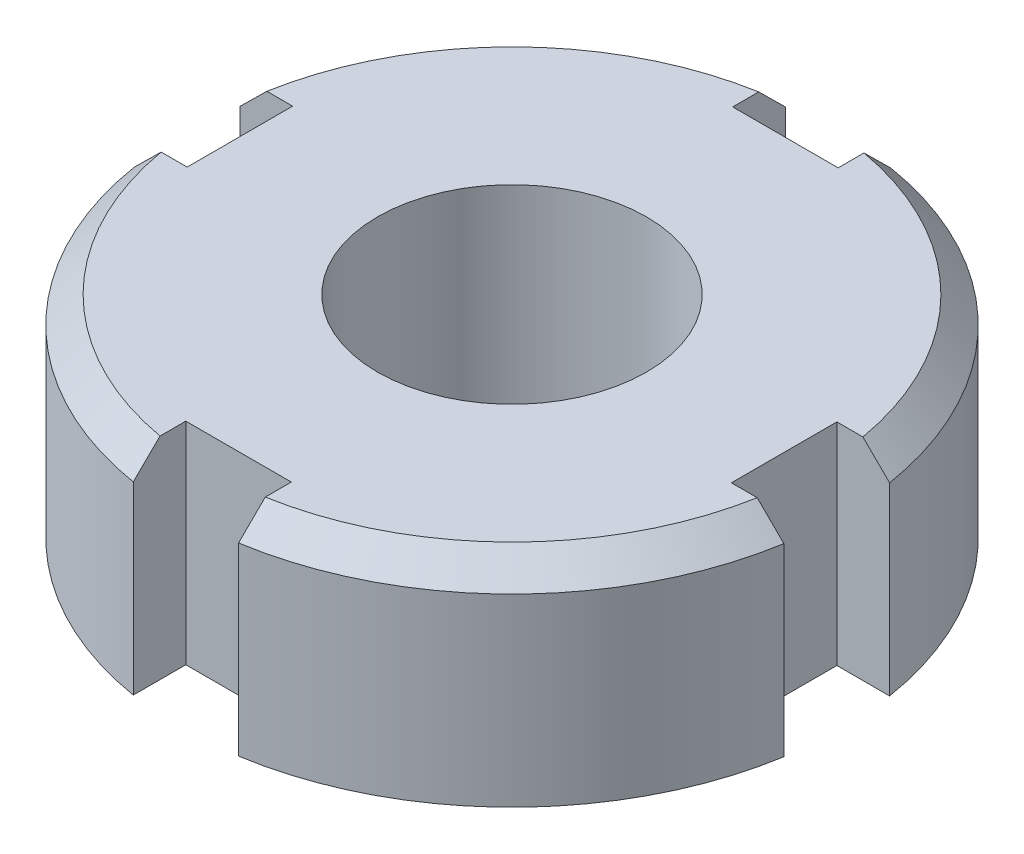
SolidWorks part; units mm, degrees
material "Plain Carbon Steel"
ref_plane "Front Plane" through (0, 0, 0) normal (0, 0, 1) x (1, 0, 0)
ref_plane "Top Plane" through (0, 0, 0) normal (0, 1, 0) x (1, 0, 0)
ref_plane "Right Plane" through (0, 0, 0) normal (1, 0, 0) x (0, 0, -1)
sketch "Sketch1" plane through (0, 0, 0) normal (0, 1, 0) x (1, 0, 0)
  circle A0 centre (0, 0) radius 12.5
  dimension "D1" = 25
extrude "Boss-Extrude1" add sketch "Sketch1" along normal mid plane 8
sketch "Sketch2" plane through (0, 0, 0) normal (0, 1, 0) x (1, 0, 0)
  line L2 (2.0251, 12.343) -> (2.0251, 10.343)
  line L3 (2.0251, 10.343) -> (-1.9749, 10.343)
  line L4 (-1.9749, 12.343) -> (-1.9749, 10.343)
  line L5 (-1.9749, 12.343) -> (-1.9749, 10.343) construction
  line L6 (12.343, 1.9749) -> (10.343, 1.9749)
  line L7 (12.343, -2.0251) -> (10.343, -2.0251)
  line L8 (10.343, -2.0251) -> (10.343, 1.9749)
  line L9 (1.9749, -12.343) -> (1.9749, -10.343)
  line L10 (-2.0251, -12.343) -> (-2.0251, -10.343)
  line L11 (-2.0251, -10.343) -> (1.9749, -10.343)
  line L12 (-12.343, -1.9749) -> (-10.343, -1.9749)
  line L13 (-12.343, 2.0251) -> (-10.343, 2.0251)
  line L14 (-10.343, 2.0251) -> (-10.343, -1.9749)
  circle A0 centre (0, 0) radius 12.5 construction
  arc A1 (2.0251, 12.3349) -> (-1.9749, 12.343) centre (0, 0) ccw
  arc A2 (12.3349, -2.0251) -> (12.343, 1.9749) centre (0, 0) ccw
  arc A3 (-2.0251, -12.3349) -> (1.9749, -12.343) centre (0, 0) ccw
  arc A4 (-12.3349, 2.0251) -> (-12.343, -1.9749) centre (0, 0) ccw
  point P0 (-1.9749, 12.343)
  point P32 (0, 0)
  dimension "D1" = 2
  dimension "D2" = 4
  dimension "D3" = 4
extrude "Cut-Extrude1" cut sketch "Sketch2" against normal through all both and the other way through all contours L7 A2 L6 L8 | L10 A3 L9 L11 | L2 A1 L4 L3 | L13 A4 L12 L14
chamfer "Chamfer1" distance 1 angle 45 4 edges at (8.8568, 4, -8.8208) (-8.8208, 4, -8.8568) (-8.8568, 4, 8.8208) (8.8208, 4, 8.8568)
sketch "Sketch3" plane through (0, 4, 0) normal (0, 1, 0) x (1, 0, 0)
  point P0 (0, 0)
hole_wizard "M12 Tapped Hole1" positions "Sketch3" profile "Sketch4" tap size "M12" standard "ISO" end condition up to next
sketch "Sketch4" plane through (0, 4, 0) normal (1, 0, 0) x (0, 0, 1)
  line L0 (0, 0) -> (0, 8)
  line L1 (0, 8) -> (5.1, 8)
  line L2 (5.1, 8) -> (5.1, 0)
  line L5 (5.1, 0) -> (0, 0)
  line L11 (0, -6.35) -> (0, 107.95) construction
  dimension "Thru Tap Drill Dia." = 10.2
  dimension "Thru Tap Drill Depth" = 8
cosmetic thread "Hole Thread1" parameters "D2"=12
